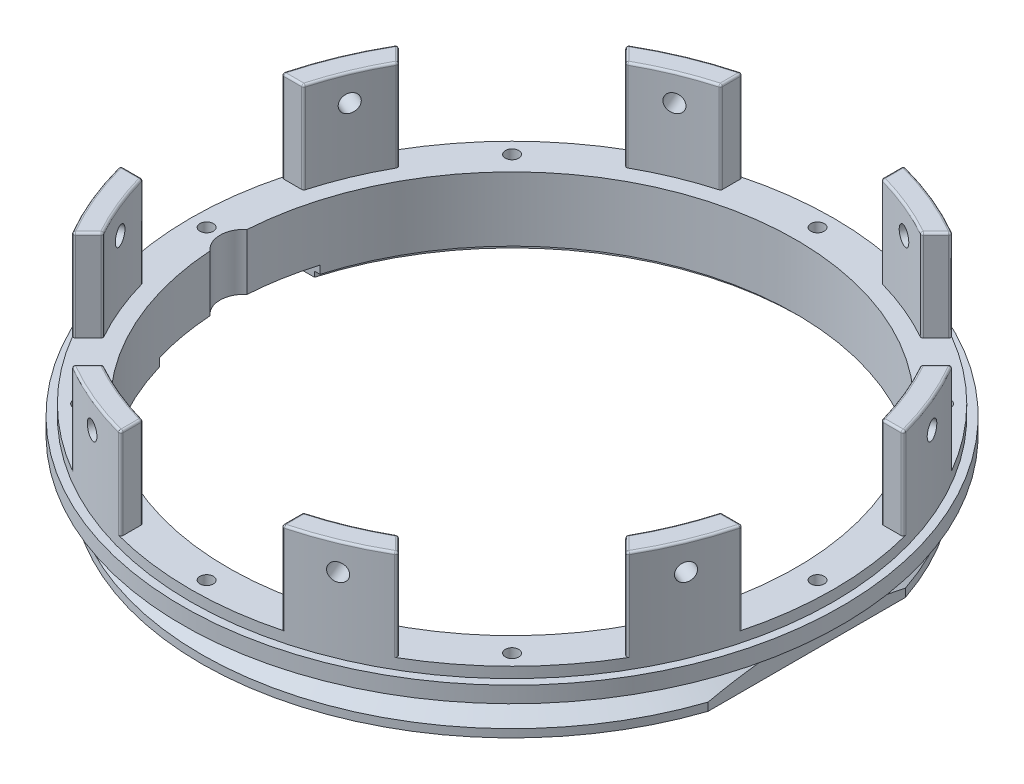
SolidWorks part; units mm, degrees
ref_plane "Ebene vorne" through (0, 0, 0) normal (0, 0, 1) x (1, 0, 0)
ref_plane "Ebene oben" through (0, 0, 0) normal (0, 1, 0) x (1, 0, 0)
ref_plane "Ebene rechts" through (0, 0, 0) normal (1, 0, 0) x (0, 0, -1)
sketch "Skizze1" plane through (0, 0, 0) normal (0, 0, 1) x (1, 0, 0)
  line L0 (-53, 1) -> (-53, 13)
  line L1 (-53, 13) -> (-56, 13)
  line L2 (-56, 13) -> (-56, 30)
  line L3 (-56, 30) -> (-60, 30)
  line L4 (-61.5, 11) -> (-61.5, 8)
  line L5 (-61.5, 8) -> (-55, 8)
  line L6 (-55, 8) -> (-55, 3.6006)
  line L7 (-55, 3.6006) -> (-58, 1.5)
  line L8 (-58, 1.5) -> (-58, 0)
  line L9 (-58, 0) -> (-54, 0)
  line L10 (-54, 0) -> (-54, 1)
  line L11 (-54, 1) -> (-53, 1)
  line L12 (-60, 30) -> (-60, 11)
  line L13 (-60, 11) -> (-61.5, 11)
  line L14 (0, 0) -> (0, 11.1018) construction
  dimension "D1" = 61.5
  dimension "D2" = 60
  dimension "D3" = 1
  dimension "D4" = 35
  dimension "D5" = 8
  dimension "D6" = 1.5
  dimension "D7" = 30
  dimension "D8" = 3
  dimension "D9" = 3
  dimension "D10" = 56
  dimension "D11" = 53
  dimension "D12" = 55
  dimension "D13" = 17
revolve "Rotation1" add sketch "Skizze1" angle 360 about L14
sketch "Skizze2" plane through (0, 0, 0) normal (1, 0, 0) x (0, 0, -1)
  line L0 (60, 30) -> (-60, 30) construction
  line L1 (15, 30) -> (-15, 30)
  line L2 (15, 30) -> (15, 13)
  line L3 (15, 13) -> (-15, 13)
  line L4 (-15, 30) -> (-15, 13)
  line L5 (0, 0) -> (0, 13) construction
  dimension "D1" = 17
  dimension "D2" = 30
extrude "Schnitt-Linear austragen1" cut sketch "Skizze2" against normal through all both and the other way through all
pattern_circular "Kreismuster1" count 8 over 360 about axis through (0, 0, 0) along (0, 1, 0) of "Schnitt-Linear austragen1"
ref_plane "Ebene1" through (-51.3557, 0, 21.2722) normal (0.9239, 0, -0.3827) x (-0.3827, 0, -0.9239)
sketch "Skizze3" plane through (-51.3557, 0, 21.2722) normal (0.9239, 0, -0.3827) x (-0.3827, 0, -0.9239)
  line L0 (0, 25) -> (0, 0) construction
  line L1 (60, 11) -> (-60, 11) construction
  circle A0 centre (0, 25) radius 1.65
  dimension "D1" = 3.3
  dimension "D2" = 14
extrude "Schnitt-Linear austragen2" cut sketch "Skizze3" against normal through all
pattern_circular "Kreismuster2" count 8 over 360 about axis through (0, 0, 0) along (0, -1, 0) of "Schnitt-Linear austragen2"
sketch "Skizze4" plane through (0, 13, 0) normal (0, 1, 0) x (1, 0, 0)
  line L0 (0, 60) -> (-7.1254, 60) construction
  line L1 (0, 57) -> (0, 60) construction
  line L2 (-57, 0) -> (57, 0) construction
  circle A0 centre (0, 57) radius 1.25
  circle A1 centre (40.3051, 40.3051) radius 1.25
  circle A2 centre (0, 0) radius 60 construction
  circle A3 centre (57, 0) radius 1.25
  circle A4 centre (40.3051, -40.3051) radius 1.25
  circle A5 centre (0, -57) radius 1.25
  circle A6 centre (-40.3051, -40.3051) radius 1.25
  circle A7 centre (-57, 0) radius 1.25
  circle A8 centre (-40.3051, 40.3051) radius 1.25
  dimension "D1" = 2.5
  dimension "D2" = 3
  dimension "D3" = 8
extrude "Schnitt-Linear austragen3" cut sketch "Skizze4" against normal up to next
sketch "Skizze5" plane through (0, 0, 0) normal (0, -1, 0) x (1, 0, 0)
  line L0 (55, 18.412) -> (55, -18.412)
  line L1 (55, 18.412) -> (58, 18.412)
  line L2 (55, -18.412) -> (58, -18.412)
  line L3 (58, 18.412) -> (58, -18.412)
  circle A0 centre (0, 0) radius 58 construction
  point P6 (58, 0)
  dimension "D1" = 3
extrude "Schnitt-Linear austragen4" cut sketch "Skizze5" against normal up to next
sketch "Skizze6" plane through (0, 0, 0) normal (0, -1, 0) x (1, 0, 0)
  line L0 (-50.8331, -15) -> (-50.8331, 15)
  line L1 (-50.8331, -15) -> (-58, -15)
  line L2 (-50.8331, 15) -> (-58, 15)
  line L3 (-58, -15) -> (-58, 15)
  arc A1 (55, 18.412) -> (55, -18.412) centre (0, 0) ccw construction
  circle A3 centre (0, 0) radius 53 construction
  dimension "D1" = 30
extrude "Schnitt-Linear austragen5" cut sketch "Skizze6" against normal blind 2.5
sketch "Skizze7" plane through (0, 13, 0) normal (0, 1, 0) x (1, 0, 0)
  line L0 (0, 0) -> (-50, 0) construction
  circle A0 centre (-50, 0) radius 4.5
  dimension "D1" = 9
  dimension "D2" = 50
extrude "Schnitt-Linear austragen6" cut sketch "Skizze7" against normal up to next
fillet "Verrundung1" radius 0.2 1 edges at (-56.5719, 2.5, 0)
fillet "Verrundung2" radius 0.4 64 edges at (29.0085, 30, 50.2217) (-50.2217, 30, -29.0085) (15, 30, 56.0242) (15, 30, -56.0242) (15, 21.5, 53.9537) (15, 21.5, -53.9537) (15, 21.5, 58.0948) (15, 21.5, -58.0948) (27.5444, 21.5, 48.7576) (-48.7576, 21.5, -27.5444) (30.4726, 21.5, 51.6858) (-51.6858, 21.5, -30.4726) (56.0242, 30, -15) (-56.0242, 30, -15) (51.7373, 30, -21.4303) (-21.4303, 30, 51.7373) (-29.0085, 30, 50.2217) (50.2217, 30, -29.0085) (-22.961, 30, 55.4328) (55.4328, 30, -22.961) (-50.2217, 30, 29.0085) (29.0085, 30, -50.2217) (21.4303, 30, -51.7373) (21.4303, 30, 51.7373) (22.961, 30, 55.4328) (22.961, 30, -55.4328) (-51.7373, 30, -21.4303) (-55.4328, 30, -22.961) (-56.0242, 30, 15) (56.0242, 30, 15) (55.4328, 30, 22.961) (-29.0085, 30, -50.2217) (50.2217, 30, 29.0085) (51.7373, 30, 21.4303) (-15, 30, 56.0242) (-15, 30, -56.0242) (-21.4303, 30, -51.7373) (-22.961, 30, -55.4328) (-51.7373, 30, 21.4303) (-55.4328, 30, 22.961) (-30.4726, 21.5, -51.6858) (51.6858, 21.5, 30.4726) (-27.5444, 21.5, -48.7576) (48.7576, 21.5, 27.5444) (-58.0948, 21.5, -15) (58.0948, 21.5, -15) (53.9537, 21.5, -15) (-53.9537, 21.5, -15) (-51.6858, 21.5, 30.4726) (30.4726, 21.5, -51.6858) (-48.7576, 21.5, 27.5444) (27.5444, 21.5, -48.7576) (-15, 21.5, 58.0948) (-15, 21.5, -58.0948) (-15, 21.5, 53.9537) (-15, 21.5, -53.9537) (-58.0948, 21.5, 15) (58.0948, 21.5, 15) (-53.9537, 21.5, 15) (53.9537, 21.5, 15) (-30.4726, 21.5, 51.6858) (51.6858, 21.5, -30.4726) (-27.5444, 21.5, 48.7576) (48.7576, 21.5, -27.5444)
